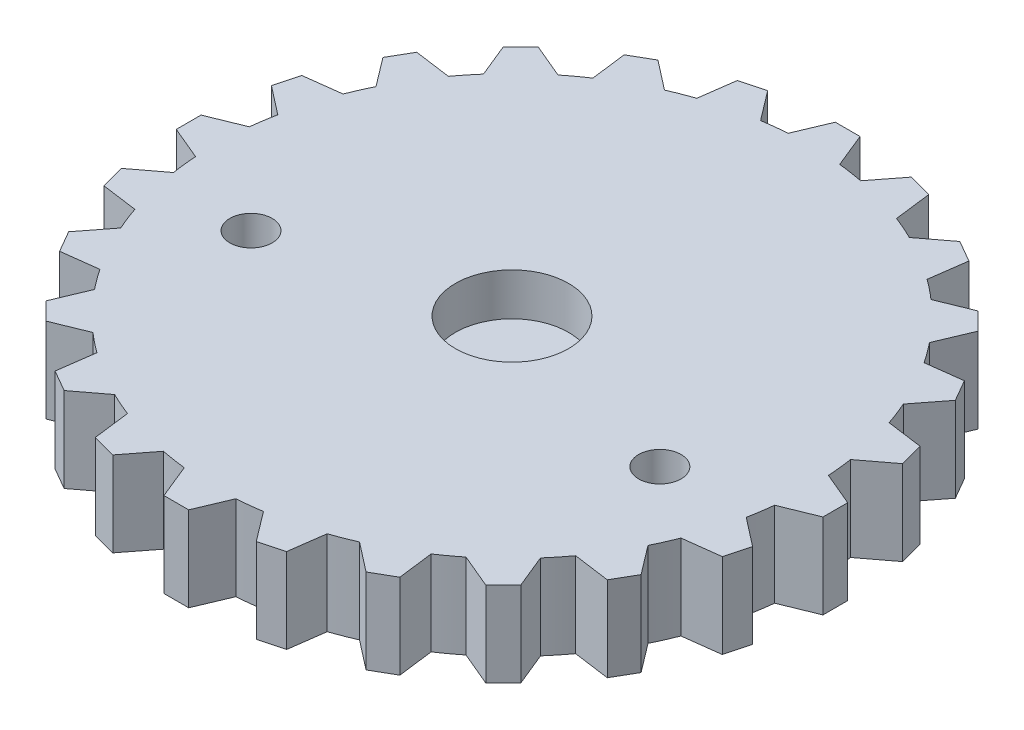
SolidWorks part; units mm, degrees
ref_plane "Front Plane" through (0, 0, 0) normal (0, 0, 1) x (1, 0, 0)
ref_plane "Top Plane" through (0, 0, 0) normal (0, 1, 0) x (1, 0, 0)
ref_plane "Right Plane" through (0, 0, 0) normal (1, 0, 0) x (0, 0, -1)
sketch "Sketch1" plane through (0, 0, 0) normal (0, 1, 0) x (1, 0, 0)
  line L111 (-0.5, 14.7462) -> (0.5, 14.7462)
  line L112 (0.5, 14.7462) -> (2, 12.5441)
  line L113 (-0.5, 14.7462) -> (-2, 12.5441)
  line L114 (6.433, 12.8885) -> (6.631, 10.2315)
  line L115 (5.567, 13.3885) -> (6.433, 12.8885)
  line L116 (5.567, 13.3885) -> (3.1669, 12.2315)
  line L117 (10.6423, 8.3132) -> (9.4853, 5.9131)
  line L118 (10.1423, 9.1792) -> (10.6423, 8.3132)
  line L119 (10.1423, 9.1792) -> (7.4853, 9.3772)
  line L120 (12, 2.2462) -> (9.798, 0.7462)
  line L121 (12, 3.2462) -> (12, 2.2462)
  line L122 (12, 3.2462) -> (9.798, 4.7462)
  line L123 (10.1423, -3.6868) -> (7.4853, -3.8849)
  line L124 (10.6423, -2.8208) -> (10.1423, -3.6868)
  line L125 (10.6423, -2.8208) -> (9.4853, -0.4208)
  line L126 (5.567, -7.8961) -> (3.1669, -6.7391)
  line L127 (6.433, -7.3961) -> (5.567, -7.8961)
  line L128 (6.433, -7.3961) -> (6.631, -4.7391)
  line L129 (-0.5, -9.2538) -> (-2, -7.0518)
  line L130 (0.5, -9.2538) -> (-0.5, -9.2538)
  line L131 (0.5, -9.2538) -> (2, -7.0518)
  line L132 (-6.433, -7.3961) -> (-6.631, -4.7391)
  line L133 (-5.567, -7.8961) -> (-6.433, -7.3961)
  line L134 (-5.567, -7.8961) -> (-3.1669, -6.7391)
  line L135 (-10.6423, -2.8208) -> (-9.4853, -0.4208)
  line L136 (-10.1423, -3.6868) -> (-10.6423, -2.8208)
  line L137 (-10.1423, -3.6868) -> (-7.4853, -3.8849)
  line L138 (-12, 3.2462) -> (-9.798, 4.7462)
  line L139 (-12, 2.2462) -> (-12, 3.2462)
  line L140 (-12, 2.2462) -> (-9.798, 0.7462)
  line L141 (-10.1423, 9.1792) -> (-7.4853, 9.3772)
  line L142 (-10.6423, 8.3132) -> (-10.1423, 9.1792)
  line L143 (-10.6423, 8.3132) -> (-9.4853, 5.9131)
  line L144 (-5.567, 13.3885) -> (-3.1669, 12.2315)
  line L145 (-6.433, 12.8885) -> (-5.567, 13.3885)
  line L146 (-6.433, 12.8885) -> (-6.631, 10.2315)
  arc A43 (-2, 12.5441) -> (-3.1669, 12.2315) centre (0, 2.7462) ccw
  arc A44 (-6.631, 10.2315) -> (-7.4853, 9.3772) centre (0, 2.7462) ccw
  arc A45 (-9.4853, 5.9131) -> (-9.798, 4.7462) centre (0, 2.7462) ccw
  arc A46 (-9.798, 0.7462) -> (-9.4853, -0.4208) centre (0, 2.7462) ccw
  arc A47 (-7.4853, -3.8849) -> (-6.631, -4.7391) centre (0, 2.7462) ccw
  arc A48 (-3.1669, -6.7391) -> (-2, -7.0518) centre (0, 2.7462) ccw
  arc A49 (2, -7.0518) -> (3.1669, -6.7391) centre (0, 2.7462) ccw
  arc A50 (6.631, -4.7391) -> (7.4853, -3.8849) centre (0, 2.7462) ccw
  arc A51 (9.4853, -0.4208) -> (9.798, 0.7462) centre (0, 2.7462) ccw
  arc A52 (9.798, 4.7462) -> (9.4853, 5.9131) centre (0, 2.7462) ccw
  arc A53 (7.4853, 9.3772) -> (6.631, 10.2315) centre (0, 2.7462) ccw
  arc A54 (3.1669, 12.2315) -> (2, 12.5441) centre (0, 2.7462) ccw
  point P6 (0, 0)
  point P8 (0, 0)
  point P9 (0, 0)
  point P12 (0, 2.7462)
  point P17 (0, 0)
  point P18 (0, 2.7462)
  point P22 (-2.5, 0.7462)
  point P63 (0, 0)
  point P68 (0, 0)
  point P69 (0, 2.7462)
  point P119 (0, 0)
  dimension "D1" = 20
  dimension "D8" = 12
sketch "Sketch2" plane through (0, 0, 0) normal (0, 1, 0) x (1, 0, 0)
  line L0 (-2, 0) -> (2, 0)
  line L1 (-23, -0.1) -> (-23, 0.1)
  line L2 (-21.1, 2) -> (-19.8997, 2)
  line L3 (-21.1, -2) -> (-19.8997, -2)
  line L4 (-20.6853, 4.6181) -> (-19.5438, 4.2472)
  line L5 (-19.4493, 8.4224) -> (-18.3078, 8.0515)
  line L6 (-21.9052, 7.0123) -> (-21.8434, 7.2025)
  line L7 (-18.2458, 10.7842) -> (-17.2748, 10.0787)
  line L8 (-15.8947, 14.0203) -> (-14.9237, 13.3148)
  line L9 (-18.6662, 13.4382) -> (-18.5486, 13.6)
  line L10 (-14.0203, 15.8947) -> (-13.3148, 14.9237)
  line L11 (-10.7842, 18.2458) -> (-10.0787, 17.2748)
  line L12 (-13.6, 18.5486) -> (-13.4382, 18.6662)
  line L13 (-8.4224, 19.4493) -> (-8.0515, 18.3078)
  line L14 (-4.6181, 20.6853) -> (-4.2472, 19.5438)
  line L15 (-7.2025, 21.8434) -> (-7.0123, 21.9052)
  line L16 (-2, 21.1) -> (-2, 19.8997)
  line L17 (2, 21.1) -> (2, 19.8997)
  line L18 (-0.1, 23) -> (0.1, 23)
  line L19 (4.6181, 20.6853) -> (4.2472, 19.5438)
  line L20 (8.4224, 19.4493) -> (8.0515, 18.3078)
  line L21 (7.0123, 21.9052) -> (7.2025, 21.8434)
  line L22 (10.7842, 18.2458) -> (10.0787, 17.2748)
  line L23 (14.0203, 15.8947) -> (13.3148, 14.9237)
  line L24 (13.4382, 18.6662) -> (13.6, 18.5486)
  line L25 (15.8947, 14.0203) -> (14.9237, 13.3148)
  line L26 (18.2458, 10.7842) -> (17.2748, 10.0787)
  line L27 (18.5486, 13.6) -> (18.6662, 13.4382)
  line L28 (19.4493, 8.4224) -> (18.3078, 8.0515)
  line L29 (20.6853, 4.6181) -> (19.5438, 4.2472)
  line L30 (21.8434, 7.2025) -> (21.9052, 7.0123)
  line L31 (21.1, 2) -> (19.8997, 2)
  line L32 (21.1, -2) -> (19.8997, -2)
  line L33 (23, 0.1) -> (23, -0.1)
  line L34 (20.6853, -4.6181) -> (19.5438, -4.2472)
  line L35 (19.4493, -8.4224) -> (18.3078, -8.0515)
  line L36 (21.9052, -7.0123) -> (21.8434, -7.2025)
  line L37 (18.2458, -10.7842) -> (17.2748, -10.0787)
  line L38 (15.8947, -14.0203) -> (14.9237, -13.3148)
  line L39 (18.6662, -13.4382) -> (18.5486, -13.6)
  line L40 (14.0203, -15.8947) -> (13.3148, -14.9237)
  line L41 (10.7842, -18.2458) -> (10.0787, -17.2748)
  line L42 (13.6, -18.5486) -> (13.4382, -18.6662)
  line L43 (8.4224, -19.4493) -> (8.0515, -18.3078)
  line L44 (4.6181, -20.6853) -> (4.2472, -19.5438)
  line L45 (7.2025, -21.8434) -> (7.0123, -21.9052)
  line L46 (2, -21.1) -> (2, -19.8997)
  line L47 (-2, -21.1) -> (-2, -19.8997)
  line L48 (0.1, -23) -> (-0.1, -23)
  line L49 (-4.6181, -20.6853) -> (-4.2472, -19.5438)
  line L50 (-8.4224, -19.4493) -> (-8.0515, -18.3078)
  line L51 (-7.0123, -21.9052) -> (-7.2025, -21.8434)
  line L52 (-10.7842, -18.2458) -> (-10.0787, -17.2748)
  line L53 (-14.0203, -15.8947) -> (-13.3148, -14.9237)
  line L54 (-13.4382, -18.6662) -> (-13.6, -18.5486)
  line L55 (-15.8947, -14.0203) -> (-14.9237, -13.3148)
  line L56 (-18.2458, -10.7842) -> (-17.2748, -10.0787)
  line L57 (-18.5486, -13.6) -> (-18.6662, -13.4382)
  line L58 (-19.4493, -8.4224) -> (-18.3078, -8.0515)
  line L59 (-20.6853, -4.6181) -> (-19.5438, -4.2472)
  line L60 (-21.8434, -7.2025) -> (-21.9052, -7.0123)
  arc A0 (-18.3078, -8.0515) -> (-17.2748, -10.0787) centre (0, 0) ccw
  arc A1 (-21.1, 2) -> (-23, 0.1) centre (-21.1, 0.1) ccw
  arc A2 (-21.1, -2) -> (-23, -0.1) centre (-21.1, -0.1) cw
  arc A3 (-20.6853, 4.6181) -> (-21.9052, 7.0123) centre (-20.0982, 6.4252) cw
  arc A4 (-19.4493, 8.4224) -> (-21.8434, 7.2025) centre (-20.0364, 6.6154) ccw
  arc A5 (-18.2458, 10.7842) -> (-18.6662, 13.4382) centre (-17.129, 12.3214) cw
  arc A6 (-15.8947, 14.0203) -> (-18.5486, 13.6) centre (-17.0115, 12.4832) ccw
  arc A7 (-14.0203, 15.8947) -> (-13.6, 18.5486) centre (-12.4832, 17.0115) cw
  arc A8 (-10.7842, 18.2458) -> (-13.4382, 18.6662) centre (-12.3214, 17.129) ccw
  arc A9 (-8.4224, 19.4493) -> (-7.2025, 21.8434) centre (-6.6154, 20.0364) cw
  arc A10 (-4.6181, 20.6853) -> (-7.0123, 21.9052) centre (-6.4252, 20.0982) ccw
  arc A11 (-2, 21.1) -> (-0.1, 23) centre (-0.1, 21.1) cw
  arc A12 (2, 21.1) -> (0.1, 23) centre (0.1, 21.1) ccw
  arc A13 (4.6181, 20.6853) -> (7.0123, 21.9052) centre (6.4252, 20.0982) cw
  arc A14 (8.4224, 19.4493) -> (7.2025, 21.8434) centre (6.6154, 20.0364) ccw
  arc A15 (10.7842, 18.2458) -> (13.4382, 18.6662) centre (12.3214, 17.129) cw
  arc A16 (14.0203, 15.8947) -> (13.6, 18.5486) centre (12.4832, 17.0115) ccw
  arc A17 (15.8947, 14.0203) -> (18.5486, 13.6) centre (17.0115, 12.4832) cw
  arc A18 (18.2458, 10.7842) -> (18.6662, 13.4382) centre (17.129, 12.3214) ccw
  arc A19 (19.4493, 8.4224) -> (21.8434, 7.2025) centre (20.0364, 6.6154) cw
  arc A20 (20.6853, 4.6181) -> (21.9052, 7.0123) centre (20.0982, 6.4252) ccw
  arc A21 (21.1, 2) -> (23, 0.1) centre (21.1, 0.1) cw
  arc A22 (21.1, -2) -> (23, -0.1) centre (21.1, -0.1) ccw
  arc A23 (20.6853, -4.6181) -> (21.9052, -7.0123) centre (20.0982, -6.4252) cw
  arc A24 (19.4493, -8.4224) -> (21.8434, -7.2025) centre (20.0364, -6.6154) ccw
  arc A25 (18.2458, -10.7842) -> (18.6662, -13.4382) centre (17.129, -12.3214) cw
  arc A26 (15.8947, -14.0203) -> (18.5486, -13.6) centre (17.0115, -12.4832) ccw
  arc A27 (14.0203, -15.8947) -> (13.6, -18.5486) centre (12.4832, -17.0115) cw
  arc A28 (10.7842, -18.2458) -> (13.4382, -18.6662) centre (12.3214, -17.129) ccw
  arc A29 (8.4224, -19.4493) -> (7.2025, -21.8434) centre (6.6154, -20.0364) cw
  arc A30 (4.6181, -20.6853) -> (7.0123, -21.9052) centre (6.4252, -20.0982) ccw
  arc A31 (2, -21.1) -> (0.1, -23) centre (0.1, -21.1) cw
  arc A32 (-2, -21.1) -> (-0.1, -23) centre (-0.1, -21.1) ccw
  arc A33 (-4.6181, -20.6853) -> (-7.0123, -21.9052) centre (-6.4252, -20.0982) cw
  arc A34 (-8.4224, -19.4493) -> (-7.2025, -21.8434) centre (-6.6154, -20.0364) ccw
  arc A35 (-10.7842, -18.2458) -> (-13.4382, -18.6662) centre (-12.3214, -17.129) cw
  arc A36 (-14.0203, -15.8947) -> (-13.6, -18.5486) centre (-12.4832, -17.0115) ccw
  arc A37 (-15.8947, -14.0203) -> (-18.5486, -13.6) centre (-17.0115, -12.4832) cw
  arc A38 (-18.2458, -10.7842) -> (-18.6662, -13.4382) centre (-17.129, -12.3214) ccw
  arc A39 (-19.4493, -8.4224) -> (-21.8434, -7.2025) centre (-20.0364, -6.6154) cw
  arc A40 (-20.6853, -4.6181) -> (-21.9052, -7.0123) centre (-20.0982, -6.4252) ccw
  arc A41 (-19.8997, -2) -> (-19.5438, -4.2472) centre (0, 0) ccw
  arc A42 (-19.5438, 4.2472) -> (-19.8997, 2) centre (0, 0) ccw
  arc A43 (-17.2748, 10.0787) -> (-18.3078, 8.0515) centre (0, 0) ccw
  arc A44 (-13.3148, 14.9237) -> (-14.9237, 13.3148) centre (0, 0) ccw
  arc A45 (-8.0515, 18.3078) -> (-10.0787, 17.2748) centre (0, 0) ccw
  arc A46 (-2, 19.8997) -> (-4.2472, 19.5438) centre (0, 0) ccw
  arc A47 (4.2472, 19.5438) -> (2, 19.8997) centre (0, 0) ccw
  arc A48 (10.0787, 17.2748) -> (8.0515, 18.3078) centre (0, 0) ccw
  arc A49 (14.9237, 13.3148) -> (13.3148, 14.9237) centre (0, 0) ccw
  arc A50 (18.3078, 8.0515) -> (17.2748, 10.0787) centre (0, 0) ccw
  arc A51 (19.8997, 2) -> (19.5438, 4.2472) centre (0, 0) ccw
  arc A52 (19.5438, -4.2472) -> (19.8997, -2) centre (0, 0) ccw
  arc A53 (17.2748, -10.0787) -> (18.3078, -8.0515) centre (0, 0) ccw
  arc A54 (13.3148, -14.9237) -> (14.9237, -13.3148) centre (0, 0) ccw
  arc A55 (8.0515, -18.3078) -> (10.0787, -17.2748) centre (0, 0) ccw
  arc A56 (2, -19.8997) -> (4.2472, -19.5438) centre (0, 0) ccw
  arc A57 (-10.0787, -17.2748) -> (-8.0515, -18.3078) centre (0, 0) ccw
  arc A58 (-4.2472, -19.5438) -> (-2, -19.8997) centre (0, 0) ccw
  arc A59 (-14.9237, -13.3148) -> (-13.3148, -14.9237) centre (0, 0) ccw
  point P6 (0, 0)
  point P10 (-23, 2)
  point P170 (0, 0)
  dimension "D1" = 40
  dimension "D4" = 1.9
  dimension "D5" = 20
sketch "Sketch3" plane through (0, 0, 0) normal (0, 1, 0) x (1, 0, 0)
  line L0 (20.6069, -4.0443) -> (20.351, -4.9991) construction
  line L1 (23.3015, -1.3115) -> (23.3015, 0.4385)
  line L2 (23.3015, 0.4385) -> (20.9515, 1.4269)
  line L3 (23.3015, -1.3115) -> (20.8737, -2.3)
  line L4 (22.621, -5.6073) -> (20.6069, -4.0443)
  line L5 (22.168, -7.2977) -> (22.621, -5.6073)
  line L6 (22.168, -7.2977) -> (19.5671, -7.6241)
  line L7 (20.3989, -11.271) -> (18.858, -9.24)
  line L8 (19.5239, -12.7866) -> (20.3989, -11.271)
  line L9 (19.5239, -12.7866) -> (16.9271, -12.4287)
  line L10 (16.7867, -16.1666) -> (15.8239, -13.8059)
  line L11 (15.5492, -17.404) -> (16.7867, -16.1666)
  line L12 (15.5492, -17.404) -> (13.1336, -16.3863)
  line L13 (12.0304, -19.9604) -> (11.7115, -17.431)
  line L14 (10.5149, -20.8354) -> (12.0304, -19.9604)
  line L15 (10.5149, -20.8354) -> (8.445, -19.2271)
  line L16 (6.4544, -22.394) -> (6.8009, -19.8682)
  line L17 (4.764, -22.8469) -> (6.4544, -22.394)
  line L18 (4.764, -22.8469) -> (3.1809, -20.7577)
  line L19 (0.4385, -23.3015) -> (1.4269, -20.9515)
  line L20 (-1.3115, -23.3015) -> (0.4385, -23.3015)
  line L21 (-1.3115, -23.3015) -> (-2.3, -20.8737)
  line L22 (-5.6073, -22.621) -> (-4.0443, -20.6069)
  line L23 (-7.2977, -22.168) -> (-5.6073, -22.621)
  line L24 (-7.2977, -22.168) -> (-7.6241, -19.5671)
  line L25 (-11.271, -20.3989) -> (-9.24, -18.858)
  line L26 (-12.7866, -19.5239) -> (-11.271, -20.3989)
  line L27 (-12.7866, -19.5239) -> (-12.4287, -16.9271)
  line L28 (-16.1666, -16.7867) -> (-13.8059, -15.8239)
  line L29 (-17.404, -15.5492) -> (-16.1666, -16.7867)
  line L30 (-17.404, -15.5492) -> (-16.3863, -13.1336)
  line L31 (-19.9604, -12.0304) -> (-17.431, -11.7115)
  line L32 (-20.8354, -10.5149) -> (-19.9604, -12.0304)
  line L33 (-20.8354, -10.5149) -> (-19.2271, -8.445)
  line L34 (-22.394, -6.4544) -> (-19.8682, -6.8009)
  line L35 (-22.8469, -4.764) -> (-22.394, -6.4544)
  line L36 (-22.8469, -4.764) -> (-20.7577, -3.1809)
  line L37 (-23.3015, -0.4385) -> (-20.9515, -1.4269)
  line L38 (-23.3015, 1.3115) -> (-23.3015, -0.4385)
  line L39 (-23.3015, 1.3115) -> (-20.8737, 2.3)
  line L40 (-22.621, 5.6073) -> (-20.6069, 4.0443)
  line L41 (-22.168, 7.2977) -> (-22.621, 5.6073)
  line L42 (-22.168, 7.2977) -> (-19.5671, 7.6241)
  line L43 (-20.3989, 11.271) -> (-18.858, 9.24)
  line L44 (-19.5239, 12.7866) -> (-20.3989, 11.271)
  line L45 (-19.5239, 12.7866) -> (-16.9271, 12.4287)
  line L46 (-16.7867, 16.1666) -> (-15.8239, 13.8059)
  line L47 (-15.5492, 17.404) -> (-16.7867, 16.1666)
  line L48 (-15.5492, 17.404) -> (-13.1336, 16.3863)
  line L49 (-12.0304, 19.9604) -> (-11.7115, 17.431)
  line L50 (-10.5149, 20.8354) -> (-12.0304, 19.9604)
  line L51 (-10.5149, 20.8354) -> (-8.445, 19.2271)
  line L52 (-6.4544, 22.394) -> (-6.8009, 19.8682)
  line L53 (-4.764, 22.8469) -> (-6.4544, 22.394)
  line L54 (-4.764, 22.8469) -> (-3.1809, 20.7577)
  line L55 (-0.4385, 23.3015) -> (-1.4269, 20.9515)
  line L56 (1.3115, 23.3015) -> (-0.4385, 23.3015)
  line L57 (1.3115, 23.3015) -> (2.3, 20.8737)
  line L58 (5.6073, 22.621) -> (4.0443, 20.6069)
  line L59 (7.2977, 22.168) -> (5.6073, 22.621)
  line L60 (7.2977, 22.168) -> (7.6241, 19.5671)
  line L61 (11.271, 20.3989) -> (9.24, 18.858)
  line L62 (12.7866, 19.5239) -> (11.271, 20.3989)
  line L63 (12.7866, 19.5239) -> (12.4287, 16.9271)
  line L64 (16.1666, 16.7867) -> (13.8059, 15.8239)
  line L65 (17.404, 15.5492) -> (16.1666, 16.7867)
  line L66 (17.404, 15.5492) -> (16.3863, 13.1336)
  line L67 (19.9604, 12.0304) -> (17.431, 11.7115)
  line L68 (20.8354, 10.5149) -> (19.9604, 12.0304)
  line L69 (20.8354, 10.5149) -> (19.2271, 8.445)
  line L70 (22.394, 6.4544) -> (19.8682, 6.8009)
  line L71 (22.8469, 4.764) -> (22.394, 6.4544)
  line L72 (22.8469, 4.764) -> (20.7577, 3.1809)
  line L73 (22.621, -5.6073) -> (20.351, -4.9991) construction
  line L74 (22.168, -7.2977) -> (19.823, -6.6694) construction
  line L75 (19.823, -6.6694) -> (19.5671, -7.6241) construction
  arc A0 (-9.24, -18.858) -> (-7.6241, -19.5671) centre (0, 0) ccw
  arc A1 (-13.8059, -15.8239) -> (-12.4287, -16.9271) centre (0, 0) ccw
  arc A2 (-17.431, -11.7115) -> (-16.3863, -13.1336) centre (0, 0) ccw
  arc A3 (-19.8682, -6.8009) -> (-19.2271, -8.445) centre (0, 0) ccw
  arc A4 (-20.9515, -1.4269) -> (-20.7577, -3.1809) centre (0, 0) ccw
  arc A5 (-20.6069, 4.0443) -> (-20.8737, 2.3) centre (0, 0) ccw
  arc A6 (-18.858, 9.24) -> (-19.5671, 7.6241) centre (0, 0) ccw
  arc A7 (-15.8239, 13.8059) -> (-16.9271, 12.4287) centre (0, 0) ccw
  arc A8 (13.8059, 15.8239) -> (12.4287, 16.9271) centre (0, 0) ccw
  arc A10 (13.8059, 15.8239) -> (12.4287, 16.9271) centre (0, 0) ccw
  arc A12 (9.24, 18.858) -> (7.6241, 19.5671) centre (0, 0) ccw
  arc A13 (13.8059, 15.8239) -> (12.4287, 16.9271) centre (0, 0) ccw
  arc A14 (17.431, 11.7115) -> (16.3863, 13.1336) centre (0, 0) ccw
  arc A15 (19.8682, 6.8009) -> (19.2271, 8.445) centre (0, 0) ccw
  arc A16 (20.9515, 1.4269) -> (20.7577, 3.1809) centre (0, 0) ccw
  arc A17 (20.6069, -4.0443) -> (20.8737, -2.3) centre (0, 0) ccw
  arc A18 (18.858, -9.24) -> (19.5671, -7.6241) centre (0, 0) ccw
  arc A19 (-4.0443, -20.6069) -> (-2.3, -20.8737) centre (0, 0) ccw
  arc A20 (1.4269, -20.9515) -> (3.1809, -20.7577) centre (0, 0) ccw
  arc A21 (6.8009, -19.8682) -> (8.445, -19.2271) centre (0, 0) ccw
  arc A22 (11.7115, -17.431) -> (13.1336, -16.3863) centre (0, 0) ccw
  arc A23 (15.8239, -13.8059) -> (16.9271, -12.4287) centre (0, 0) ccw
  arc A24 (-20.6069, 4.0443) -> (-20.8737, 2.3) centre (0, 0) ccw
  arc A25 (-20.6069, 4.0443) -> (-20.8737, 2.3) centre (0, 0) ccw
  arc A26 (-20.6069, 4.0443) -> (-20.8737, 2.3) centre (0, 0) ccw
  arc A27 (-18.858, 9.24) -> (-19.5671, 7.6241) centre (0, 0) ccw
  arc A28 (-18.858, 9.24) -> (-19.5671, 7.6241) centre (0, 0) ccw
  arc A29 (-18.858, 9.24) -> (-19.5671, 7.6241) centre (0, 0) ccw
  arc A30 (-15.8239, 13.8059) -> (-16.9271, 12.4287) centre (0, 0) ccw
  arc A31 (-15.8239, 13.8059) -> (-16.9271, 12.4287) centre (0, 0) ccw
  arc A32 (-15.8239, 13.8059) -> (-16.9271, 12.4287) centre (0, 0) ccw
  arc A33 (-11.7115, 17.431) -> (-13.1336, 16.3863) centre (0, 0) ccw
  arc A34 (-11.7115, 17.431) -> (-13.1336, 16.3863) centre (0, 0) ccw
  arc A35 (-11.7115, 17.431) -> (-13.1336, 16.3863) centre (0, 0) ccw
  arc A36 (-11.7115, 17.431) -> (-13.1336, 16.3863) centre (0, 0) ccw
  arc A37 (-6.8009, 19.8682) -> (-8.445, 19.2271) centre (0, 0) ccw
  arc A38 (-6.8009, 19.8682) -> (-8.445, 19.2271) centre (0, 0) ccw
  arc A39 (-6.8009, 19.8682) -> (-8.445, 19.2271) centre (0, 0) ccw
  arc A40 (-6.8009, 19.8682) -> (-8.445, 19.2271) centre (0, 0) ccw
  arc A41 (-1.4269, 20.9515) -> (-3.1809, 20.7577) centre (0, 0) ccw
  arc A42 (-1.4269, 20.9515) -> (-3.1809, 20.7577) centre (0, 0) ccw
  arc A43 (-1.4269, 20.9515) -> (-3.1809, 20.7577) centre (0, 0) ccw
  arc A44 (-1.4269, 20.9515) -> (-3.1809, 20.7577) centre (0, 0) ccw
  arc A45 (4.0443, 20.6069) -> (2.3, 20.8737) centre (0, 0) ccw
  arc A46 (4.0443, 20.6069) -> (2.3, 20.8737) centre (0, 0) ccw
  arc A47 (4.0443, 20.6069) -> (2.3, 20.8737) centre (0, 0) ccw
  arc A48 (4.0443, 20.6069) -> (2.3, 20.8737) centre (0, 0) ccw
  arc A49 (9.24, 18.858) -> (7.6241, 19.5671) centre (0, 0) ccw
  arc A50 (9.24, 18.858) -> (7.6241, 19.5671) centre (0, 0) ccw
  arc A51 (9.24, 18.858) -> (7.6241, 19.5671) centre (0, 0) ccw
  arc A52 (13.8059, 15.8239) -> (12.4287, 16.9271) centre (0, 0) ccw
  arc A53 (17.431, 11.7115) -> (16.3863, 13.1336) centre (0, 0) ccw
  arc A54 (19.8682, 6.8009) -> (19.2271, 8.445) centre (0, 0) ccw
  arc A55 (20.9515, 1.4269) -> (20.7577, 3.1809) centre (0, 0) ccw
  arc A56 (20.9515, 1.4269) -> (20.7577, 3.1809) centre (0, 0) ccw
  arc A57 (20.9515, 1.4269) -> (20.7577, 3.1809) centre (0, 0) ccw
  arc A58 (20.6069, -4.0443) -> (20.8737, -2.3) centre (0, 0) ccw
  arc A59 (20.6069, -4.0443) -> (20.8737, -2.3) centre (0, 0) ccw
  arc A60 (20.6069, -4.0443) -> (20.8737, -2.3) centre (0, 0) ccw
  arc A61 (18.858, -9.24) -> (19.5671, -7.6241) centre (0, 0) ccw
  arc A62 (18.858, -9.24) -> (19.5671, -7.6241) centre (0, 0) ccw
  arc A63 (18.858, -9.24) -> (19.5671, -7.6241) centre (0, 0) ccw
  arc A64 (15.8239, -13.8059) -> (16.9271, -12.4287) centre (0, 0) ccw
  arc A65 (15.8239, -13.8059) -> (16.9271, -12.4287) centre (0, 0) ccw
  arc A66 (15.8239, -13.8059) -> (16.9271, -12.4287) centre (0, 0) ccw
  arc A67 (11.7115, -17.431) -> (13.1336, -16.3863) centre (0, 0) ccw
  arc A68 (11.7115, -17.431) -> (13.1336, -16.3863) centre (0, 0) ccw
  arc A69 (11.7115, -17.431) -> (13.1336, -16.3863) centre (0, 0) ccw
  arc A70 (6.8009, -19.8682) -> (8.445, -19.2271) centre (0, 0) ccw
  arc A71 (6.8009, -19.8682) -> (8.445, -19.2271) centre (0, 0) ccw
  arc A72 (6.8009, -19.8682) -> (8.445, -19.2271) centre (0, 0) ccw
  arc A73 (1.4269, -20.9515) -> (3.1809, -20.7577) centre (0, 0) ccw
  arc A74 (1.4269, -20.9515) -> (3.1809, -20.7577) centre (0, 0) ccw
  arc A75 (1.4269, -20.9515) -> (3.1809, -20.7577) centre (0, 0) ccw
  arc A76 (-4.0443, -20.6069) -> (-2.3, -20.8737) centre (0, 0) ccw
  arc A77 (-4.0443, -20.6069) -> (-2.3, -20.8737) centre (0, 0) ccw
  arc A78 (-4.0443, -20.6069) -> (-2.3, -20.8737) centre (0, 0) ccw
  arc A79 (-9.24, -18.858) -> (-7.6241, -19.5671) centre (0, 0) ccw
  arc A80 (-9.24, -18.858) -> (-7.6241, -19.5671) centre (0, 0) ccw
  arc A81 (-9.24, -18.858) -> (-7.6241, -19.5671) centre (0, 0) ccw
  arc A82 (-13.8059, -15.8239) -> (-12.4287, -16.9271) centre (0, 0) ccw
  arc A83 (-13.8059, -15.8239) -> (-12.4287, -16.9271) centre (0, 0) ccw
  arc A84 (-13.8059, -15.8239) -> (-12.4287, -16.9271) centre (0, 0) ccw
  arc A85 (-17.431, -11.7115) -> (-16.3863, -13.1336) centre (0, 0) ccw
  arc A86 (-17.431, -11.7115) -> (-16.3863, -13.1336) centre (0, 0) ccw
  arc A87 (-17.431, -11.7115) -> (-16.3863, -13.1336) centre (0, 0) ccw
  arc A88 (-19.8682, -6.8009) -> (-19.2271, -8.445) centre (0, 0) ccw
  arc A89 (-19.8682, -6.8009) -> (-19.2271, -8.445) centre (0, 0) ccw
  arc A90 (-19.8682, -6.8009) -> (-19.2271, -8.445) centre (0, 0) ccw
  arc A91 (-20.9515, -1.4269) -> (-20.7577, -3.1809) centre (0, 0) ccw
  arc A92 (-20.9515, -1.4269) -> (-20.7577, -3.1809) centre (0, 0) ccw
  arc A93 (-20.9515, -1.4269) -> (-20.7577, -3.1809) centre (0, 0) ccw
  point P6 (0, 0)
  point P7 (0, -12.952)
  point P8 (-6.2727, 0)
  point P9 (11.4668, 0)
  point P10 (0, 0)
  point P108 (0, 0)
  dimension "D1" = 42
  dimension "D4" = 24
  dimension "1." = 1.75
  dimension "2.5" = 2.35
extrude "Boss-Extrude5" add sketch "Sketch3" along normal blind 6 separate body
extrude "Boss-Extrude6" add sketch "Sketch1" along normal blind 3 separate body
sketch "Sketch4" plane through (0, 6, 0) normal (0, 1, 0) x (1, 0, 0)
  circle A0 centre (0, 0) radius 4
  dimension "D1" = 8
extrude "Cut-Extrude1" cut sketch "Sketch4" against normal blind 10
sketch "Sketch5" plane through (0, 6, 0) normal (0, 1, 0) x (1, 0, 0)
  line L0 (-14.4568, -4) -> (14.4568, -4) construction
  circle A0 centre (-14.4568, -4) radius 1.5
  circle A1 centre (0, 0) radius 4 construction
  circle A2 centre (14.4568, -4) radius 1.5
  dimension "D1" = 3
  dimension "D2" = 15
  dimension "D3" = 3
  dimension "D4" = 15
extrude "Cut-Extrude2" cut sketch "Sketch5" against normal through all
